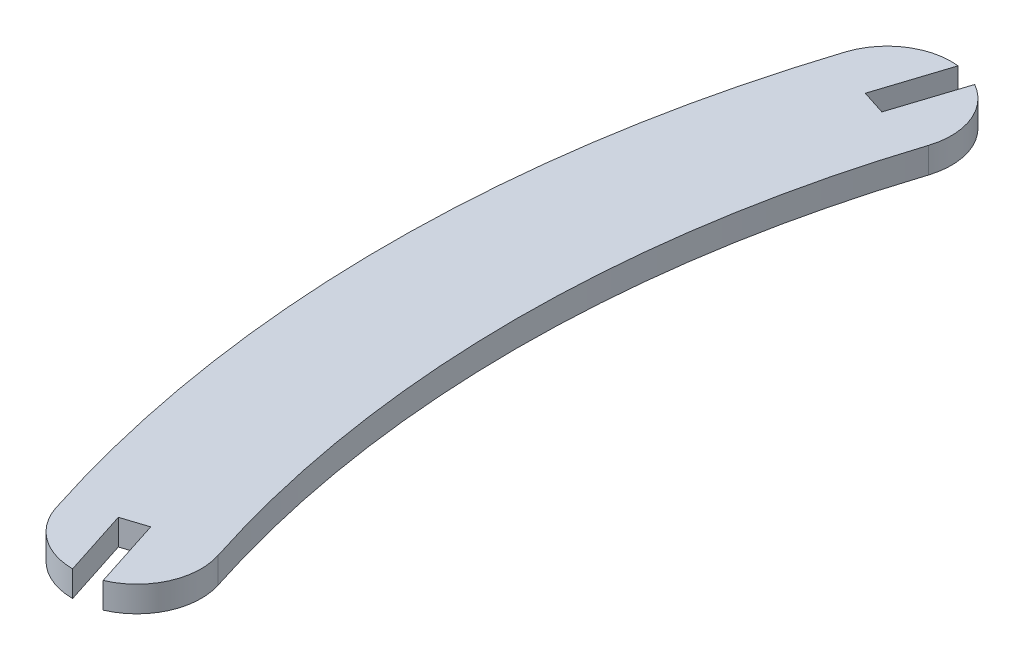
SolidWorks part; units mm, degrees
ref_plane "Alzado" through (0, 0, 0) normal (0, 0, 1) x (1, 0, 0)
ref_plane "Planta" through (0, 0, 0) normal (0, 1, 0) x (1, 0, 0)
ref_plane "Vista lateral" through (0, 0, 0) normal (1, 0, 0) x (0, 0, -1)
sketch "Croquis2" plane through (0, 0, 0) normal (0, 1, 0) x (1, 0, 0)
  line L0 (-134.7902, 51.2016) -> (-137.4304, 43.0169)
  line L1 (-137.4304, 43.0169) -> (-134.5753, 42.0959)
  line L2 (-134.5753, 42.0959) -> (-131.9351, 50.2806)
  line L3 (-133.3161, 50.8853) -> (-136.0028, 42.5564) construction
  line L4 (-135.9663, -42.6697) -> (-137.4304, -38.1309) construction
  line L5 (-132.6623, -50.6403) -> (-135.3025, -42.4556)
  line L6 (-135.3025, -42.4556) -> (-138.1576, -43.3766)
  line L7 (-138.1576, -43.3766) -> (-135.6186, -51.2475)
  line L8 (-133.3161, -50.8853) -> (-135.9663, -42.6697) construction
  arc A0 (-142.7564, -46.05) -> (-142.7564, 46.05) centre (0, 0) cw
  arc A1 (-142.7564, 46.05) -> (-134.7902, 51.2016) centre (-135.6186, 43.7475) cw
  arc A2 (-128.4808, 41.445) -> (-128.4808, -41.445) centre (0, 0) ccw
  arc A3 (-142.7564, -46.05) -> (-135.6186, -51.2475) centre (-135.6186, -43.7475) ccw
  arc A4 (-135.6186, -51.2475) -> (-133.3161, -50.8853) centre (-135.6186, -43.7475) ccw construction
  arc A5 (-132.6623, -50.6403) -> (-128.4808, -41.445) centre (-135.6186, -43.7475) ccw
  arc A6 (-133.3161, -50.8853) -> (-132.6623, -50.6403) centre (-135.6186, -43.7475) ccw construction
  arc A7 (-134.7902, 51.2016) -> (-133.3161, 50.8853) centre (-135.6186, 43.7475) cw construction
  arc A8 (-131.9351, 50.2806) -> (-128.4808, 41.445) centre (-135.6186, 43.7475) cw
  arc A9 (-133.3161, 50.8853) -> (-131.9351, 50.2806) centre (-135.6186, 43.7475) cw construction
  point P9 (-135, 0)
  point P23 (0, 0)
  point P24 (0, 0)
  point P25 (0, 0)
  dimension "D1" = 150
  dimension "D2" = 7.5
  dimension "D3" = 92.1
  dimension "D4" = 3
  dimension "D5" = 8.6
  dimension "D6" = 8.6
  dimension "D7" = 3
  dimension "D8" = 8.6
extrude "Saliente-Extruir1" add sketch "Croquis2" along normal blind 3
equation "\"A\"= 3"
equation "\"B\"= 8.6"
equation "\"C\"= 150"
equation "\"D1@Croquis2\"=\"C\""
equation "\"D7@Croquis2\"=\"A\""
equation "\"D8@Croquis2\"=\"B\""
equation "\"D6@Croquis2\"=\"B\""
equation "\"D5@Croquis2\"=\"B\""
equation "\"D4@Croquis2\"=\"A\""
